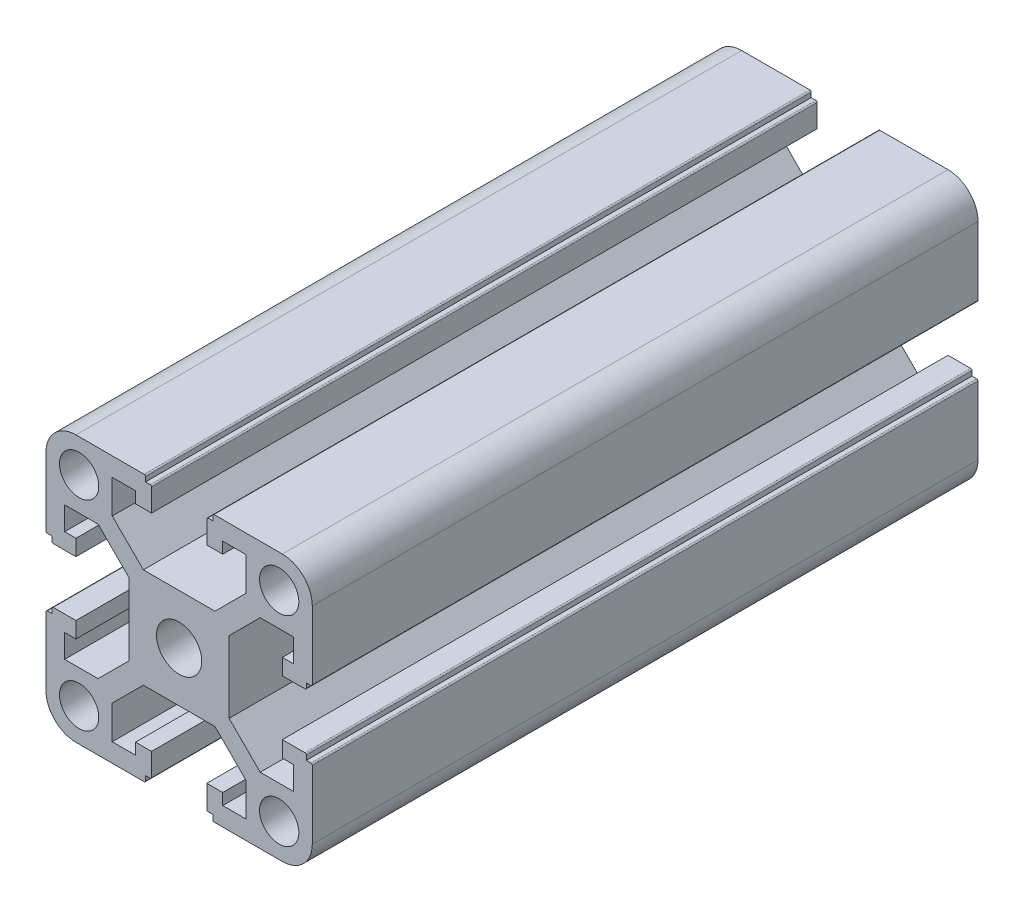
SolidWorks part; units mm, degrees
material "6061-T6 (SS)"
ref_plane "前视基准面" through (0, 0, 0) normal (0, 0, 1) x (1, 0, 0)
ref_plane "上视基准面" through (0, 0, 0) normal (0, 1, 0) x (1, 0, 0)
ref_plane "右视基准面" through (0, 0, 0) normal (1, 0, 0) x (0, 0, -1)
ref_plane "基准面1" through (0, 0, 50) normal (0, 0, 1) x (1, 0, 0)
sketch "草图1" plane through (0, 0, 50) normal (0, 0, 1) x (1, 0, 0)
  line L0 (-1518.245, 3588.0043) -> (-1518.245, 3582.9756)
  line L1 (-1518.245, 3582.9756) -> (-1522.9163, 3578.3043)
  line L2 (-1522.9163, 3578.3043) -> (-1533.6737, 3578.3043)
  line L3 (-1533.6737, 3578.3043) -> (-1538.345, 3582.9756)
  line L4 (-1538.345, 3582.9756) -> (-1538.345, 3588.0043)
  line L5 (-1538.345, 3588.0043) -> (-1534.845, 3588.0043)
  line L6 (-1534.845, 3588.0043) -> (-1534.845, 3586.3043)
  line L7 (-1534.845, 3586.3043) -> (-1532.445, 3586.3043)
  line L8 (-1532.445, 3586.3043) -> (-1532.445, 3589.7043)
  line L9 (-1532.645, 3589.9043) -> (-1533.345, 3589.9043)
  line L10 (-1533.345, 3589.9043) -> (-1533.345, 3590.6043)
  line L11 (-1533.545, 3590.8043) -> (-1543.795, 3590.8043)
  line L12 (-1548.295, 3586.3043) -> (-1548.295, 3576.0543)
  line L13 (-1548.095, 3575.8543) -> (-1547.395, 3575.8543)
  line L14 (-1547.395, 3575.8543) -> (-1547.395, 3575.1543)
  line L15 (-1547.195, 3574.9543) -> (-1543.795, 3574.9543)
  line L16 (-1543.795, 3574.9543) -> (-1543.795, 3577.3543)
  line L17 (-1543.795, 3577.3543) -> (-1545.495, 3577.3543)
  line L18 (-1545.495, 3577.3543) -> (-1545.495, 3580.8543)
  line L19 (-1545.495, 3580.8543) -> (-1540.4663, 3580.8543)
  line L20 (-1540.4663, 3580.8543) -> (-1535.795, 3576.183)
  line L21 (-1535.795, 3576.183) -> (-1535.795, 3565.4256)
  line L22 (-1535.795, 3565.4256) -> (-1540.4663, 3560.7543)
  line L23 (-1540.4663, 3560.7543) -> (-1545.495, 3560.7543)
  line L24 (-1545.495, 3560.7543) -> (-1545.495, 3564.2543)
  line L25 (-1545.495, 3564.2543) -> (-1543.795, 3564.2543)
  line L26 (-1543.795, 3564.2543) -> (-1543.795, 3566.6543)
  line L27 (-1543.795, 3566.6543) -> (-1547.195, 3566.6543)
  line L28 (-1547.395, 3566.4543) -> (-1547.395, 3565.7543)
  line L29 (-1547.395, 3565.7543) -> (-1548.095, 3565.7543)
  line L30 (-1548.295, 3565.5543) -> (-1548.295, 3555.3043)
  line L31 (-1543.795, 3550.8043) -> (-1533.545, 3550.8043)
  line L32 (-1533.345, 3551.0043) -> (-1533.345, 3551.7043)
  line L33 (-1533.345, 3551.7043) -> (-1532.645, 3551.7043)
  line L34 (-1532.445, 3551.9043) -> (-1532.445, 3555.3043)
  line L35 (-1532.445, 3555.3043) -> (-1534.845, 3555.3043)
  line L36 (-1534.845, 3555.3043) -> (-1534.845, 3553.6043)
  line L37 (-1534.845, 3553.6043) -> (-1538.345, 3553.6043)
  line L38 (-1538.345, 3553.6043) -> (-1538.345, 3558.633)
  line L39 (-1538.345, 3558.633) -> (-1533.6737, 3563.3043)
  line L40 (-1533.6737, 3563.3043) -> (-1522.9163, 3563.3043)
  line L41 (-1522.9163, 3563.3043) -> (-1518.245, 3558.633)
  line L42 (-1518.245, 3558.633) -> (-1518.245, 3553.6043)
  line L43 (-1518.245, 3553.6043) -> (-1521.745, 3553.6043)
  line L44 (-1521.745, 3553.6043) -> (-1521.745, 3555.3043)
  line L45 (-1521.745, 3555.3043) -> (-1524.145, 3555.3043)
  line L46 (-1524.145, 3555.3043) -> (-1524.145, 3551.9043)
  line L47 (-1523.945, 3551.7043) -> (-1523.245, 3551.7043)
  line L48 (-1523.245, 3551.7043) -> (-1523.245, 3551.0043)
  line L49 (-1523.045, 3550.8043) -> (-1512.795, 3550.8043)
  line L50 (-1508.295, 3555.3043) -> (-1508.295, 3565.5543)
  line L51 (-1508.495, 3565.7543) -> (-1509.195, 3565.7543)
  line L52 (-1509.195, 3565.7543) -> (-1509.195, 3566.4543)
  line L53 (-1509.395, 3566.6543) -> (-1512.795, 3566.6543)
  line L54 (-1512.795, 3566.6543) -> (-1512.795, 3564.2543)
  line L55 (-1512.795, 3564.2543) -> (-1511.095, 3564.2543)
  line L56 (-1511.095, 3564.2543) -> (-1511.095, 3560.7543)
  line L57 (-1511.095, 3560.7543) -> (-1516.1237, 3560.7543)
  line L58 (-1516.1237, 3560.7543) -> (-1520.795, 3565.4256)
  line L59 (-1520.795, 3565.4256) -> (-1520.795, 3576.183)
  line L60 (-1520.795, 3576.183) -> (-1516.1237, 3580.8543)
  line L61 (-1516.1237, 3580.8543) -> (-1511.095, 3580.8543)
  line L62 (-1511.095, 3580.8543) -> (-1511.095, 3577.3543)
  line L63 (-1511.095, 3577.3543) -> (-1512.795, 3577.3543)
  line L64 (-1512.795, 3577.3543) -> (-1512.795, 3574.9543)
  line L65 (-1512.795, 3574.9543) -> (-1509.395, 3574.9543)
  line L66 (-1509.195, 3575.1543) -> (-1509.195, 3575.8543)
  line L67 (-1509.195, 3575.8543) -> (-1508.495, 3575.8543)
  line L68 (-1508.295, 3576.0543) -> (-1508.295, 3586.3043)
  line L69 (-1512.795, 3590.8043) -> (-1523.045, 3590.8043)
  line L70 (-1523.245, 3590.6043) -> (-1523.245, 3589.9043)
  line L71 (-1523.245, 3589.9043) -> (-1523.945, 3589.9043)
  line L72 (-1524.145, 3589.7043) -> (-1524.145, 3586.3043)
  line L73 (-1524.145, 3586.3043) -> (-1521.745, 3586.3043)
  line L74 (-1521.745, 3586.3043) -> (-1521.745, 3588.0043)
  line L75 (-1521.745, 3588.0043) -> (-1518.245, 3588.0043)
  circle A0 centre (-1513.27, 3555.7793) radius 2.95
  circle A1 centre (-1528.295, 3570.8043) radius 3.4
  circle A2 centre (-1513.27, 3585.8293) radius 2.95
  arc A3 (-1532.445, 3589.7043) -> (-1532.645, 3589.9043) centre (-1532.645, 3589.7043) ccw
  arc A4 (-1533.345, 3590.6043) -> (-1533.545, 3590.8043) centre (-1533.545, 3590.6043) ccw
  arc A5 (-1543.795, 3590.8043) -> (-1548.295, 3586.3043) centre (-1543.795, 3586.3043) ccw
  arc A6 (-1548.295, 3576.0543) -> (-1548.095, 3575.8543) centre (-1548.095, 3576.0543) ccw
  arc A7 (-1547.395, 3575.1543) -> (-1547.195, 3574.9543) centre (-1547.195, 3575.1543) ccw
  arc A8 (-1547.195, 3566.6543) -> (-1547.395, 3566.4543) centre (-1547.195, 3566.4543) ccw
  arc A9 (-1548.095, 3565.7543) -> (-1548.295, 3565.5543) centre (-1548.095, 3565.5543) ccw
  arc A10 (-1548.295, 3555.3043) -> (-1543.795, 3550.8043) centre (-1543.795, 3555.3043) ccw
  arc A11 (-1533.545, 3550.8043) -> (-1533.345, 3551.0043) centre (-1533.545, 3551.0043) ccw
  arc A12 (-1532.645, 3551.7043) -> (-1532.445, 3551.9043) centre (-1532.645, 3551.9043) ccw
  arc A13 (-1524.145, 3551.9043) -> (-1523.945, 3551.7043) centre (-1523.945, 3551.9043) ccw
  arc A14 (-1523.245, 3551.0043) -> (-1523.045, 3550.8043) centre (-1523.045, 3551.0043) ccw
  arc A15 (-1512.795, 3550.8043) -> (-1508.295, 3555.3043) centre (-1512.795, 3555.3043) ccw
  arc A16 (-1508.295, 3565.5543) -> (-1508.495, 3565.7543) centre (-1508.495, 3565.5543) ccw
  arc A17 (-1509.195, 3566.4543) -> (-1509.395, 3566.6543) centre (-1509.395, 3566.4543) ccw
  arc A18 (-1509.395, 3574.9543) -> (-1509.195, 3575.1543) centre (-1509.395, 3575.1543) ccw
  arc A19 (-1508.495, 3575.8543) -> (-1508.295, 3576.0543) centre (-1508.495, 3576.0543) ccw
  arc A20 (-1508.295, 3586.3043) -> (-1512.795, 3590.8043) centre (-1512.795, 3586.3043) ccw
  arc A21 (-1523.045, 3590.8043) -> (-1523.245, 3590.6043) centre (-1523.045, 3590.6043) ccw
  arc A22 (-1523.945, 3589.9043) -> (-1524.145, 3589.7043) centre (-1523.945, 3589.7043) ccw
  circle A23 centre (-1543.32, 3585.8293) radius 2.95
  circle A24 centre (-1543.32, 3555.7793) radius 2.95
extrude "凸台-拉伸1" add sketch "草图1" against normal mid plane 100
ref_plane "基准面2" through (-1528.295, 0, 0) normal (1, 0, 0) x (0, 0, -1)
ref_plane "基准面3" through (0, 3570.8043, 0) normal (0, 1, 0) x (1, 0, 0)
